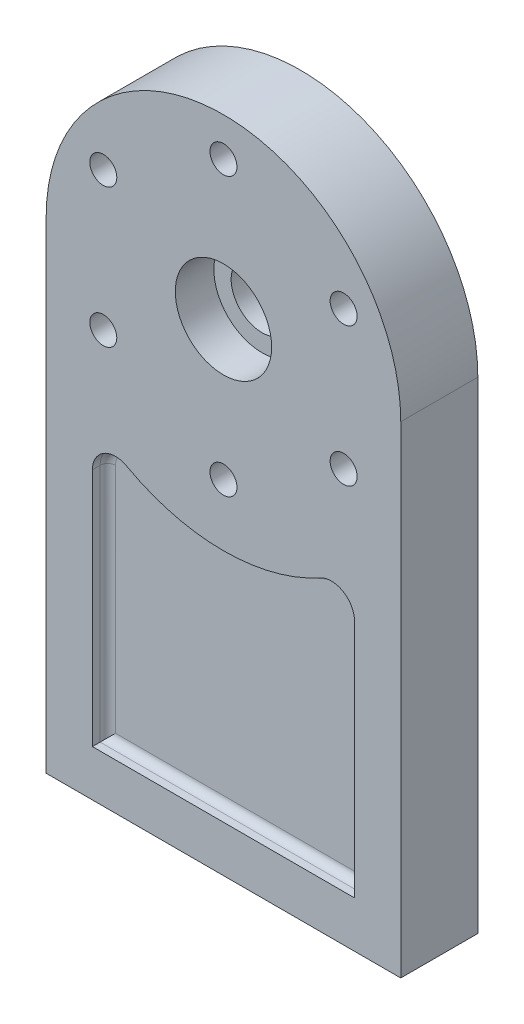
SolidWorks part; units mm, degrees
ref_plane "Front Plane" through (0, 0, 0) normal (0, 0, 1) x (1, 0, 0)
ref_plane "Top Plane" through (0, 0, 0) normal (0, 1, 0) x (1, 0, 0)
ref_plane "Right Plane" through (0, 0, 0) normal (1, 0, 0) x (0, 0, -1)
sketch "Sketch1" plane through (0, 0, 0) normal (0, 0, 1) x (1, 0, 0)
  line L0 (46, 125) -> (46, 0)
  line L1 (46, 0) -> (-46, 0)
  line L2 (-46, 0) -> (-46, 125)
  arc A0 (46, 125) -> (-46, 125) centre (0, 125) ccw
  circle A1 centre (0, 125) radius 8
  dimension "D2" = 92
  dimension "D3" = 16
  dimension "D1" = 125
extrude "Boss-Extrude1" add sketch "Sketch1" along normal mid plane 20
sketch "Sketch2" plane through (0, 0, 10) normal (0, 0, 1) x (1, 0, 0)
  circle A0 centre (0, 125) radius 12.5
  dimension "D1" = 25
extrude "Cut-Extrude1" cut sketch "Sketch2" against normal blind 10
sketch "Sketch3" plane through (0, 0, 10) normal (0, 0, 1) x (1, 0, 0)
  circle A0 centre (0, 161) radius 3.5
  circle A1 centre (0, 125) radius 36 construction
  point P5 (0, 0)
  point P6 (0, 164.0818)
  dimension "D1" = 72
  dimension "D2" = 7
extrude "Cut-Extrude2" cut sketch "Sketch3" against normal through all
sketch "Sketch4" plane through (0, 0, -10) normal (0, 0, -1) x (-1, 0, 0)
  circle A0 centre (0, 161) radius 6
  dimension "D1" = 12
extrude "Cut-Extrude3" cut sketch "Sketch4" against normal blind 6
pattern_circular "CirPattern1" count 6 over 360 about axis through (0, 125, 0) along (0, 0, 1) of "Cut-Extrude3", "Cut-Extrude2"
hole_wizard "Tap Drill for M10x1.25 Tap2" positions "Sketch9" profile "Sketch10" hole size "M10x1.25" standard "ISO"
sketch "Sketch9" plane through (0, 0, 0) normal (0, -1, 0) x (-1, 0, 0)
  line L0 (46, 10) -> (-46, 10) construction
  line L1 (46, -10) -> (46, 10) construction
  point P0 (30, 0)
  point P2 (-30, 0)
  dimension "D1" = 60
  dimension "D2" = 10
  dimension "D3" = 16
sketch "Sketch10" plane through (-30, 0, 0) normal (1, 0, 0) x (0, 0, -1)
  line L0 (0, 0) -> (0, 26.6438)
  line L1 (0, 26.6438) -> (4.4, 24)
  line L2 (4.4, 24) -> (4.4, 0)
  line L5 (4.4, 0) -> (0, 0)
  line L10 (0, 26.6438) -> (-4.4, 24) construction
  line L11 (0, -6.35) -> (0, 107.95) construction
  dimension "Hole Dia." = 8.8
  dimension "Hole Depth" = 24
  dimension "Drill Angle" = 118
sketch "Sketch11" plane through (0, 0, 10) normal (0, 0, 1) x (1, 0, 0)
  line L6 (-34, 125) -> (-34, 12)
  line L7 (-34, 12) -> (34, 12)
  line L8 (34, 12) -> (34, 125)
  line L9 (-34, 74.2063) -> (-34, 12)
  line L10 (-34, 12) -> (34, 12)
  line L11 (34, 12) -> (34, 74.2063)
  arc A0 (-25.1034, 79.4608) -> (25.1034, 79.4608) centre (0, 125) ccw
  arc A1 (25.1034, 79.4608) -> (34, 74.2063) centre (28, 74.2063) cw
  arc A2 (-25.1034, 79.4608) -> (-34, 74.2063) centre (-28, 74.2063) ccw
  dimension "D1" = 104
  dimension "D3" = 6
  dimension "D2" = 12
extrude "Cut-Extrude4" cut sketch "Sketch11" against normal blind 4
fillet "Fillet1" radius 2 6 edges at (34, 43.1031, 6) (0, 12, 6) (-34, 43.1031, 6) (-31.0513, 79.3725, 6) (0, 73, 6) (31.0513, 79.3725, 6)
mirror "Mirror1" about plane through (0, 0, 0) normal (0, 0, 1) of "Cut-Extrude4", "Fillet1"
